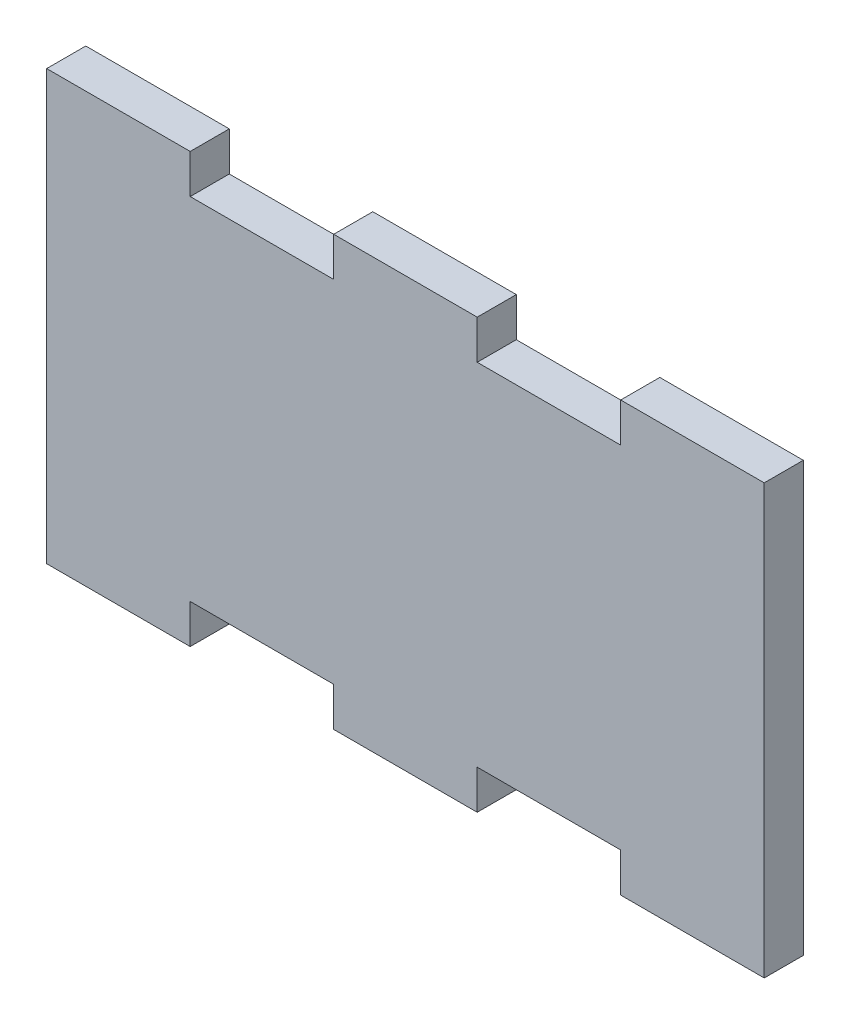
SolidWorks part; units mm, degrees
ref_plane "Front Plane" through (0, 0, 0) normal (0, 0, 1) x (1, 0, 0)
ref_plane "Top Plane" through (0, 0, 0) normal (0, 1, 0) x (1, 0, 0)
ref_plane "Right Plane" through (0, 0, 0) normal (1, 0, 0) x (0, 0, -1)
sketch "Sketch1" plane through (0, 0, 0) normal (0, 0, 1) x (1, 0, 0)
  line L1 (0, 0) -> (29.14, 0)
  line L2 (0, 0) -> (0, 14.24)
  line L3 (11.656, 14.24) -> (23.312, 14.24)
  line L4 (29.14, 0) -> (29.14, 14.24)
  line L6 (0, 14.24) -> (0, 17.415)
  line L7 (0, 17.415) -> (11.656, 17.415)
  line L8 (11.656, 14.24) -> (11.656, 17.415)
  line L10 (29.14, 14.24) -> (29.14, 17.415)
  line L11 (29.14, 17.415) -> (23.312, 17.415)
  line L12 (23.312, 14.24) -> (23.312, 17.415)
  dimension "D1" = 29.14
  dimension "D2" = 11.656
  dimension "D4" = 3.175
  dimension "D5" = 14.24
extrude "Boss-Extrude1" add sketch "Sketch1" along normal blind 3.175
mirror "Mirror1" about plane through (0, 0, 3.175) normal (0, 1, 0) of bodies 101
mirror "Mirror3" about plane through (29.14, 14.24, 3.175) normal (-1, 0, 0) of bodies 102
